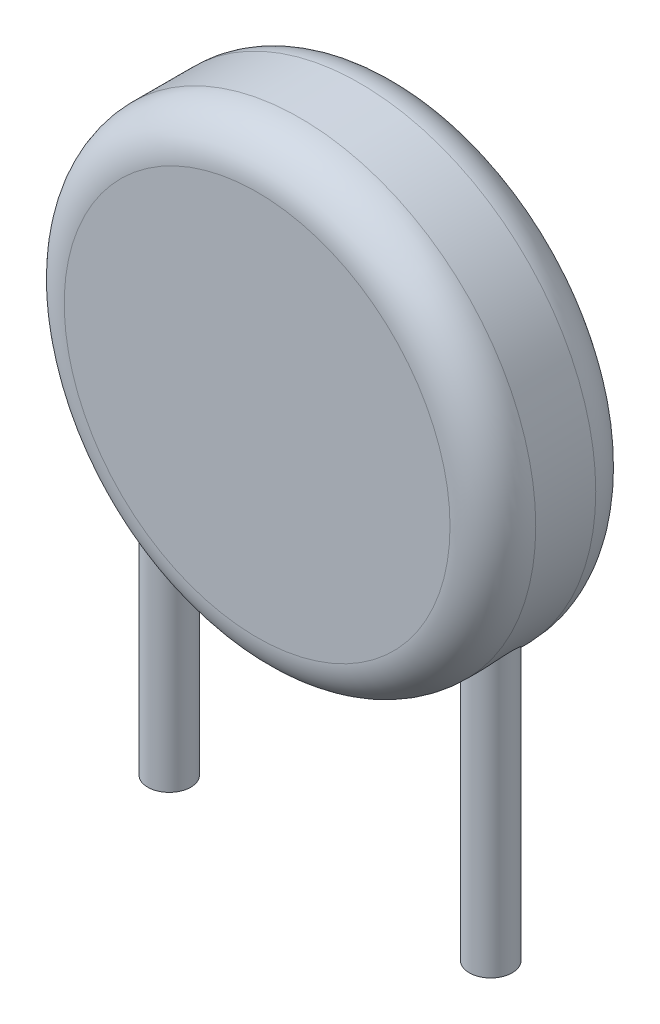
SolidWorks part; units mm, degrees
ref_plane "Ön Düzlem" through (0, 0, 0) normal (0, 0, 1) x (1, 0, 0)
ref_plane "Üst Düzlem" through (0, 0, 0) normal (0, 1, 0) x (1, 0, 0)
ref_plane "Sağ Düzlem" through (0, 0, 0) normal (1, 0, 0) x (0, 0, -1)
sketch "Çizim1" plane through (0, 0, 0) normal (0, 0, 1) x (1, 0, 0)
  circle A0 centre (0, 0) radius 5.5
  dimension "D1" = 11
extrude "Yükseklik-Ekstrüzyon1" add sketch "Çizim1" along normal blind 3.4
ref_plane "Düzlem1" through (0, -10, 0) normal (0, 1, 0) x (1, 0, 0)
sketch "Çizim2" plane through (0, -10, 0) normal (0, 1, 0) x (1, 0, 0)
  circle A0 centre (-3.75, -1.7) radius 0.5
  circle A1 centre (3.75, -1.7) radius 0.5
  dimension "D1" = 1
  dimension "D3" = 1
extrude "Yükseklik-Ekstrüzyon2" add sketch "Çizim2" along normal blind 7
fillet "Radyus1" radius 1 2 edges at (5.5, 0, 0) (5.5, 0, 3.4)
sketch "Çizim3" plane through (0, 0, 0) normal (0, 0, -1) x (-1, 0, 0)
  text T0 "MOV-10DxxxK" font "Consolas" height in points 3
extrude "Yükseklik-Ekstrüzyon3" add sketch "Çizim3" along normal blind 0.01
